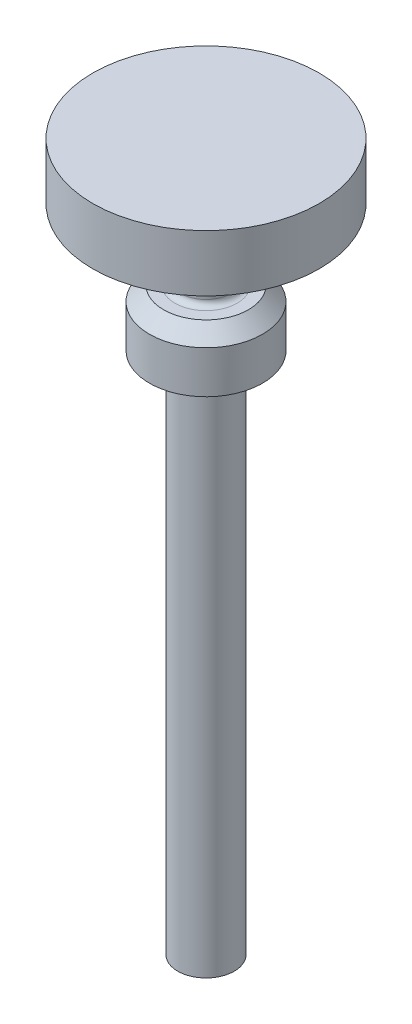
SolidWorks part; units mm, degrees
ref_plane "Front Plane" through (0, 0, 0) normal (0, 0, 1) x (1, 0, 0)
ref_plane "Top Plane" through (0, 0, 0) normal (0, 1, 0) x (1, 0, 0)
ref_plane "Right Plane" through (0, 0, 0) normal (1, 0, 0) x (0, 0, -1)
sketch "Sketch2" plane through (0, 0, 0) normal (0, 0, 1) x (1, 0, 0)
  line L0 (0, 0) -> (0, 25)
  line L1 (0, 25) -> (4, 25)
  line L2 (4, 25) -> (4, 23)
  line L3 (4, 23) -> (0.9, 23)
  line L4 (0.9, 23) -> (0.9, 20.5)
  line L5 (0.9, 20.5) -> (2, 20.5)
  line L6 (2, 20.5) -> (2, 18.5)
  line L7 (2, 18.5) -> (1, 18.5)
  line L8 (1, 18.5) -> (1, 0)
  line L9 (1, 0) -> (0, 0)
  point P11 (0.9, 21.75)
  point P12 (0.8, 23)
  dimension "D1" = 2.5
  dimension "D2" = 2
  dimension "D3" = 25
  dimension "D4" = 4
  dimension "D5" = 2
  dimension "D6" = 1
  dimension "D7" = 0.9
  dimension "D8" = 2
revolve "Revolve1" add sketch "Sketch2" angle 360 about L0
chamfer "Chamfer1" distance 0.5 angle 45 1 edges at (0, 20.5, -2)
fillet "Fillet1" radius 0.2 3 edges at (0, 18.5, -1) (0, 20.5, -0.9) (0, 23, -0.9)
